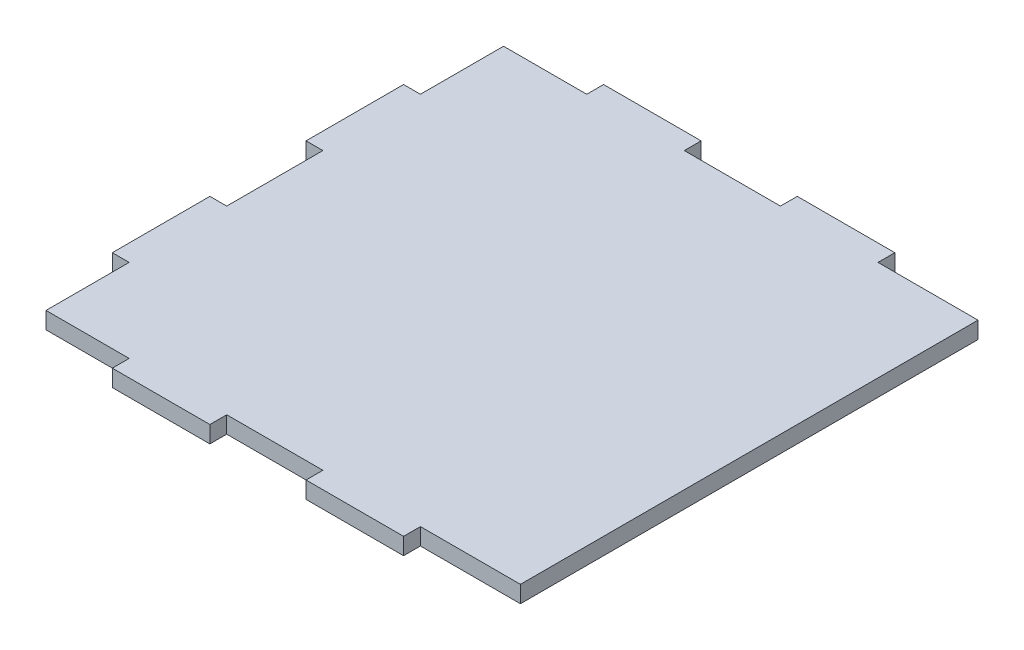
SolidWorks part; units mm, degrees
material "Maple"
ref_plane "Front Plane" through (0, 0, 0) normal (0, 0, 1) x (1, 0, 0)
ref_plane "Top Plane" through (0, 0, 0) normal (0, 1, 0) x (1, 0, 0)
ref_plane "Right Plane" through (0, 0, 0) normal (1, 0, 0) x (0, 0, -1)
sketch "Sketch1" plane through (0, 0, 0) normal (0, 1, 0) x (1, 0, 0)
  line L0 (209.25, 350) -> (278.75, 350)
  line L1 (71.25, 0) -> (140.75, 0)
  line L2 (0, 71.25) -> (0, 140.75)
  line L3 (71.25, 350) -> (140.75, 350)
  line L4 (350, 12) -> (350, 338)
  line L7 (12, 338) -> (71.25, 338)
  line L8 (71.25, 350) -> (71.25, 338)
  line L11 (350, 338) -> (278.75, 338)
  line L12 (278.75, 350) -> (278.75, 338)
  line L14 (140.75, 350) -> (140.75, 338)
  line L15 (140.75, 338) -> (209.25, 338)
  line L16 (209.25, 350) -> (209.25, 338)
  line L18 (209.25, 0) -> (209.25, 12)
  line L19 (140.75, 12) -> (209.25, 12)
  line L20 (140.75, 0) -> (140.75, 12)
  line L21 (278.75, 0) -> (278.75, 12)
  line L22 (350, 12) -> (278.75, 12)
  line L23 (71.25, 0) -> (71.25, 12)
  line L24 (12, 12) -> (71.25, 12)
  line L25 (71.25, 0) -> (140.75, 0)
  line L26 (209.25, 0) -> (278.75, 0)
  line L27 (209.25, 0) -> (278.75, 0)
  line L28 (0, 209.25) -> (0, 278.75)
  line L31 (0, 278.75) -> (12, 278.75)
  line L32 (12, 338) -> (12, 278.75)
  line L33 (0, 209.25) -> (12, 209.25)
  line L35 (0, 140.75) -> (12, 140.75)
  line L36 (12, 209.25) -> (12, 140.75)
  line L39 (0, 71.25) -> (12, 71.25)
  line L40 (12, 12) -> (12, 71.25)
  dimension "D2" = 69.5
  dimension "D3" = 71.25
  dimension "D4" = 69.5
  dimension "D5" = 71.25
  dimension "D6" = 69.5
  dimension "D7" = 12
  dimension "D8" = 71.25
  dimension "D9" = 69.5
  dimension "D10" = 71.25
  dimension "D11" = 69.5
  dimension "D12" = 12
  dimension "D13" = 350
  dimension "D14" = 69.5
  dimension "D15" = 326
  dimension "D16" = 68.5
extrude "Boss-Extrude1" add sketch "Sketch1" along normal blind 12 contours L40 L24 L23 L1 L20 L19 L18 L26 L21 L22 L4 L11 L12 L0 L16 L15 L14 L3 L8 L7 L32 L31 L28 L33 L36 L35 L2 L39
